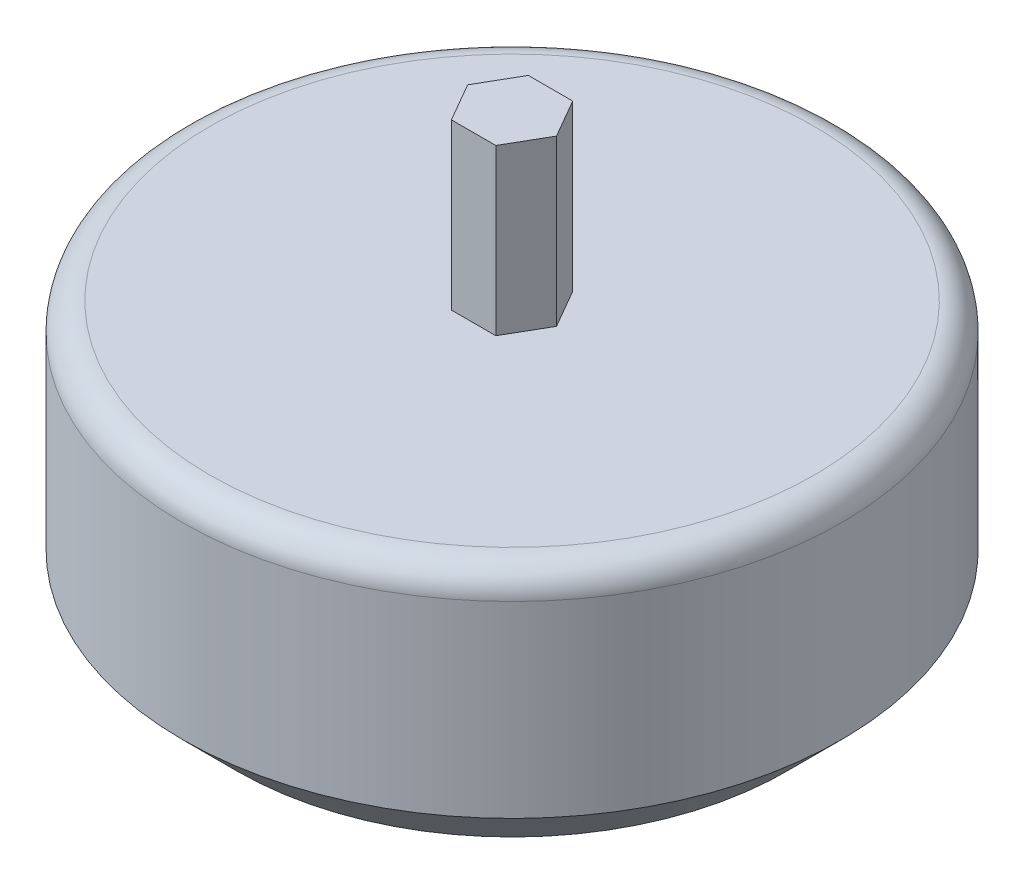
SolidWorks part; units mm, degrees
material "Acrylic (Medium-high impact)"
ref_plane "Front Plane" through (0, 0, 0) normal (0, 0, 1) x (1, 0, 0)
ref_plane "Top Plane" through (0, 0, 0) normal (0, 1, 0) x (1, 0, 0)
ref_plane "Right Plane" through (0, 0, 0) normal (1, 0, 0) x (0, 0, -1)
sketch "Sketch1" plane through (0, 0, 0) normal (0, 1, 0) x (1, 0, 0)
  circle A0 centre (0, 0) radius 60
  dimension "D1" = 120
extrude "Boss-Extrude1" add sketch "Sketch1" along normal blind 49.2
sketch "Sketch2" plane through (0, 49.2, 0) normal (0, 1, 0) x (1, 0, 0)
  line L1 (-4.0415, 7) -> (-8.0829, 0)
  line L2 (-8.0829, 0) -> (-4.0415, -7)
  line L3 (-4.0415, -7) -> (4.0415, -7)
  line L4 (4.0415, -7) -> (8.0829, 0)
  line L5 (8.0829, 0) -> (4.0415, 7)
  line L6 (4.0415, 7) -> (-4.0415, 7)
  circle A0 centre (0, 0) radius 7 construction
  dimension "D1" = 14
extrude "Boss-Extrude3" add sketch "Sketch2" along normal blind 30
fillet "Fillet1" radius 5 1 edges at (0, 49.2, 60)
sketch "Sketch3" plane through (0, 0, 0) normal (0, -1, 0) x (1, 0, 0)
  line L0 (0, 0) -> (0, -36) construction
  line L1 (0, 0) -> (-18, -31.1769) construction
  circle A0 centre (0, 0) radius 36 construction
  point P3 (-18, 31.1769)
  point P4 (18, 31.1769)
  point P5 (-18, -31.1769)
  point P6 (18, -31.1769)
  dimension "D1" = 72
  dimension "D2" = 30
hole_wizard "Tap Drill for M5x0.8 Tap1" positions "Sketch4" profile "Sketch5" hole size "M5x0.8" standard "ANSI Metric"
sketch "Sketch4" plane through (0, 0, 0) normal (0, -1, 0) x (-1, 0, 0)
  point P0 (-18, 31.1769)
  point P3 (18, 31.1769)
  point P6 (18, -31.1769)
  point P9 (-18, -31.1769)
sketch "Sketch5" plane through (18, 0, -31.1769) normal (1, 0, 0) x (0, 0, -1)
  line L0 (0, 0) -> (0, 6.2618)
  line L1 (0, 6.2618) -> (2.1, 5)
  line L2 (2.1, 5) -> (2.1, 0)
  line L5 (2.1, 0) -> (0, 0)
  line L10 (0, 6.2618) -> (-2.1, 5) construction
  line L11 (0, -6.35) -> (0, 107.95) construction
  dimension "Hole Dia." = 4.2
  dimension "Hole Depth" = 5
  dimension "Drill Angle" = 118
chamfer "Chamfer1" distance 10 angle 45 1 edges at (0, 0, 60)
